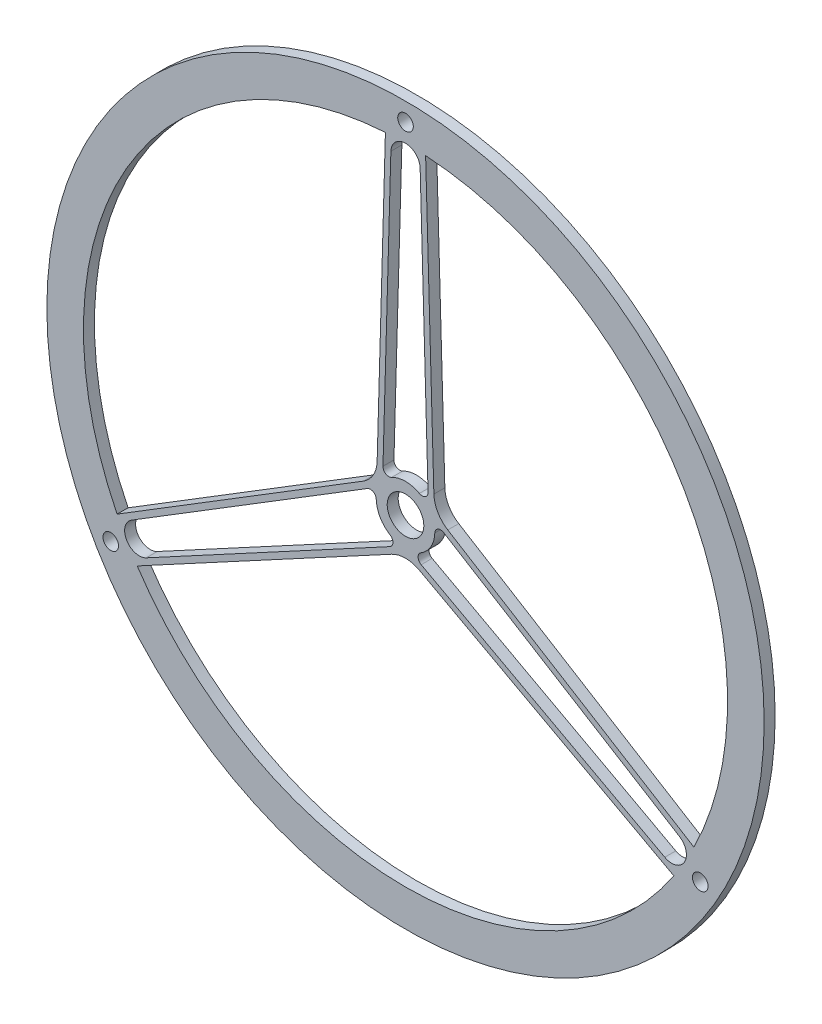
SolidWorks part; units mm, degrees
material "PVC 0.007 Plasticized"
ref_plane "Front Plane" through (0, 0, 0) normal (0, 0, 1) x (1, 0, 0)
ref_plane "Top Plane" through (0, 0, 0) normal (0, 1, 0) x (1, 0, 0)
ref_plane "Right Plane" through (0, 0, 0) normal (1, 0, 0) x (0, 0, -1)
sketch "Sketch1" plane through (0, 0, 0) normal (0, 0, 1) x (1, 0, 0)
  line L0 (-12.6948, 0.3629) -> (-12.5857, 4.1794)
  line L1 (0, 0) -> (0, 133.35) construction
  line L2 (12.6948, 0.3629) -> (12.5857, 4.1794)
  line L3 (-8.8864, 133.604) -> (-8.7199, 139.4276)
  line L4 (8.8864, 133.604) -> (8.7199, 139.4276)
  line L5 (9.9381, 7.9072) -> (6.3474, 133.5314)
  line L6 (-9.9381, 7.9072) -> (-6.3474, 133.5314)
  line L7 (-10.1559, 0.2903) -> (-6.3474, 133.5314) construction
  line L8 (10.1559, 0.2903) -> (6.3474, 133.5314) construction
  line L9 (-6.0332, -11.1755) -> (-2.6734, -12.9893)
  line L10 (2.6734, -12.9893) -> (112.4679, -72.2627)
  line L11 (12.5857, 4.1794) -> (118.8153, -61.2687)
  line L12 (12.4989, 7.2163) -> (120.1476, -59.1062)
  line L13 (111.2613, -74.4978) -> (116.3879, -77.2655)
  line L14 (120.1476, -59.1062) -> (125.1078, -62.1621)
  line L15 (-12.4989, 7.2163) -> (-120.1476, -59.1062)
  line L16 (-12.5857, 4.1794) -> (-118.8153, -61.2687)
  line L17 (-2.6734, -12.9893) -> (-112.4679, -72.2627)
  line L18 (6.0332, -11.1755) -> (2.6734, -12.9893)
  line L19 (-120.1476, -59.1062) -> (-125.1078, -62.1621)
  line L20 (-111.2613, -74.4978) -> (-116.3879, -77.2655)
  line L21 (-12.4989, 7.2163) -> (-8.8864, 133.604)
  line L22 (-12.6948, 0.3629) -> (-8.8864, 133.604) construction
  line L23 (0, -14.4325) -> (111.2613, -74.4978)
  line L24 (0, -14.4325) -> (-111.2613, -74.4978)
  line L25 (12.4989, 7.2163) -> (8.8864, 133.604)
  line L26 (12.6948, 0.3629) -> (8.8864, 133.604) construction
  line L27 (0, 0) -> (0, 147.6375) construction
  line L28 (0, 0) -> (127.8578, -73.8188) construction
  line L29 (0, 0) -> (-127.8578, -73.8187) construction
  circle A0 centre (0, 0) radius 7.9375
  arc A1 (-12.6948, 0.3629) -> (-6.0332, -11.1755) centre (0, 0) ccw
  circle A2 centre (0, 0) radius 139.7
  circle A3 centre (0, 0) radius 147.6375 construction
  circle A4 centre (0, 0) radius 155.575
  circle A5 centre (0, 0) radius 133.35 construction
  arc A8 (-6.3474, 133.5314) -> (6.3474, 133.5314) centre (0, 133.35) cw
  arc A9 (9.9381, 7.9072) -> (-9.9381, 7.9072) centre (0, 0) ccw
  arc A10 (118.8153, -61.2687) -> (112.4679, -72.2627) centre (115.4845, -66.675) cw
  arc A11 (-112.4679, -72.2627) -> (-118.8153, -61.2687) centre (-115.4845, -66.675) cw
  arc A12 (6.0332, -11.1755) -> (12.6948, 0.3629) centre (0, 0) ccw
  point P45 (0, 0)
  point P50 (0, 0)
  dimension "D1" = 311.15
  dimension "D2" = 295.275
  dimension "D3" = 279.4
  dimension "D4" = 25.4
  dimension "D5" = 15.875
  dimension "D6" = 266.7
  dimension "D7" = 6.35
  dimension "D8" = 2.54
  dimension "D9" = 2.54
  dimension "D10" = 3
  dimension "D11" = 3
extrude "Boss-Extrude1" add sketch "Sketch1" against normal blind 4.7625 contours A4 A2 | L18 A12 L2 L11 A10 A2 L14 L12 L25 L4 A8 L5 A9 L6 L3 L21 L15 L19 A11 L16 L0 A1 L9 L17 L20 L24 L23 L13 L10 A0
fillet "Fillet1" radius 12.7 3 edges at (0, -14.4325, -2.3813) (12.4989, 7.2163, -2.3813) (-12.4989, 7.2163, -2.3813)
fillet "Fillet4" radius 2.54 6 edges at (12.5857, 4.1794, -2.3813) (2.6734, -12.9893, -2.3813) (-2.6734, -12.9893, -2.3813) (-12.5857, 4.1794, -2.3813) (-9.9381, 7.9072, -2.3813) (9.9381, 7.9072, -2.3813)
hole_wizard "H (0.266) Diameter Hole1" positions "Sketch3" profile "Sketch4" hole size "H" standard "ANSI Inch" end condition through all
sketch "Sketch3" plane through (0, 0, 0) normal (0, 0, 1) x (1, 0, 0)
  point P0 (0, 147.6375)
  point P3 (127.8578, -73.8188)
  point P6 (-127.8578, -73.8187)
sketch "Sketch4" plane through (0, 147.6375, 0) normal (1, 0, 0) x (0, -1, 0)
  line L0 (0, 0) -> (0, 4.7625)
  line L1 (0, 4.7625) -> (3.3782, 4.7625)
  line L2 (3.3782, 4.7625) -> (3.3782, 0)
  line L5 (3.3782, 0) -> (0, 0)
  line L11 (0, -6.35) -> (0, 107.95) construction
  dimension "Thru Hole Dia." = 6.7564
  dimension "Thru Hole Depth" = 4.7625
